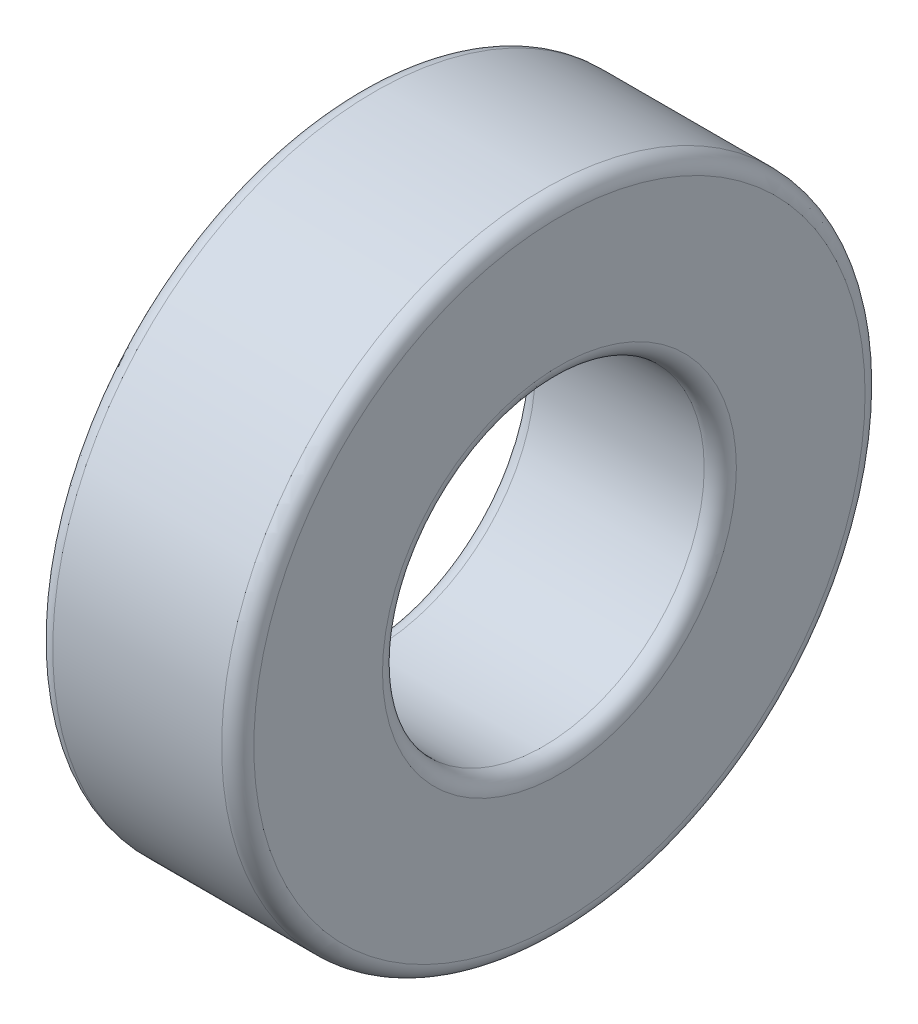
SolidWorks part; units mm, degrees
ref_plane "Alzado" through (0, 0, 0) normal (0, 0, 1) x (1, 0, 0)
ref_plane "Planta" through (0, 0, 0) normal (0, 1, 0) x (1, 0, 0)
ref_plane "Vista lateral" through (0, 0, 0) normal (1, 0, 0) x (0, 0, -1)
sketch "Croquis1" plane through (0, 0, 0) normal (1, 0, 0) x (0, 0, -1)
  circle A0 centre (0, 0) radius 8
  circle A1 centre (0, 0) radius 4
  point P4 (0, 0)
  dimension "D1" = 16
  dimension "D2" = 8
extrude "Saliente-Extruir1" add sketch "Croquis1" along normal blind 5
fillet "Redondeo1" radius 0.4 4 edges at (0, 0, -8) (0, 0, -4) (5, 0, -4) (5, 0, -8)
